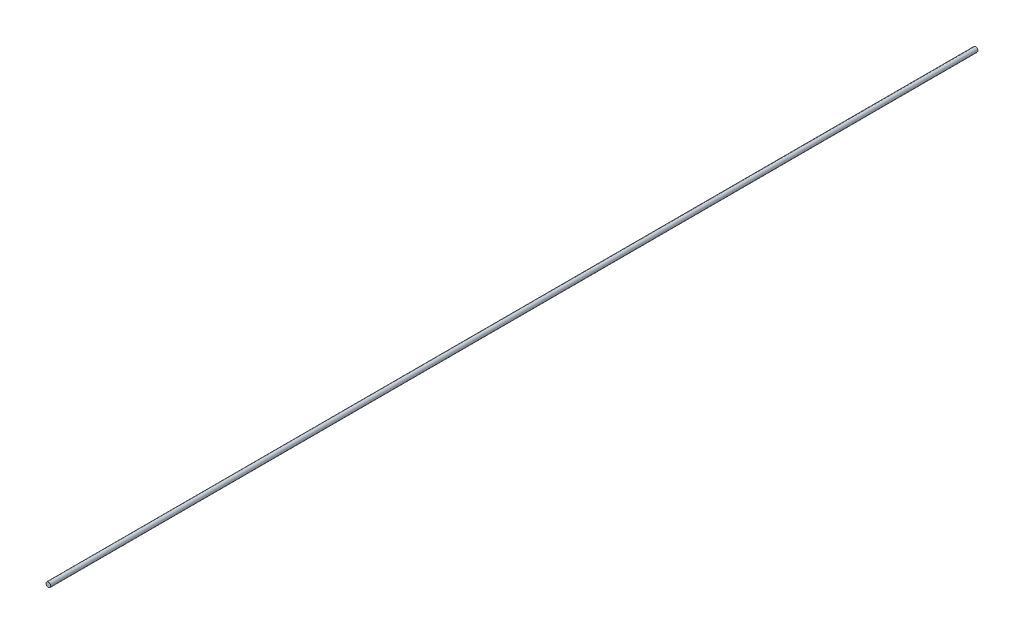
SolidWorks part; units mm, degrees
ref_plane "Plan de face" through (0, 0, 0) normal (0, 0, 1) x (1, 0, 0)
ref_plane "Plan de dessus" through (0, 0, 0) normal (0, 1, 0) x (1, 0, 0)
ref_plane "Plan de droite" through (0, 0, 0) normal (1, 0, 0) x (0, 0, -1)
sketch "Esquisse1" plane through (0, 0, 0) normal (0, 0, 1) x (1, 0, 0)
  circle A0 centre (0, 0) radius 5
  dimension "D1" = 10
extrude "Boss.-Extru.1" add sketch "Esquisse1" along normal blind 1980
